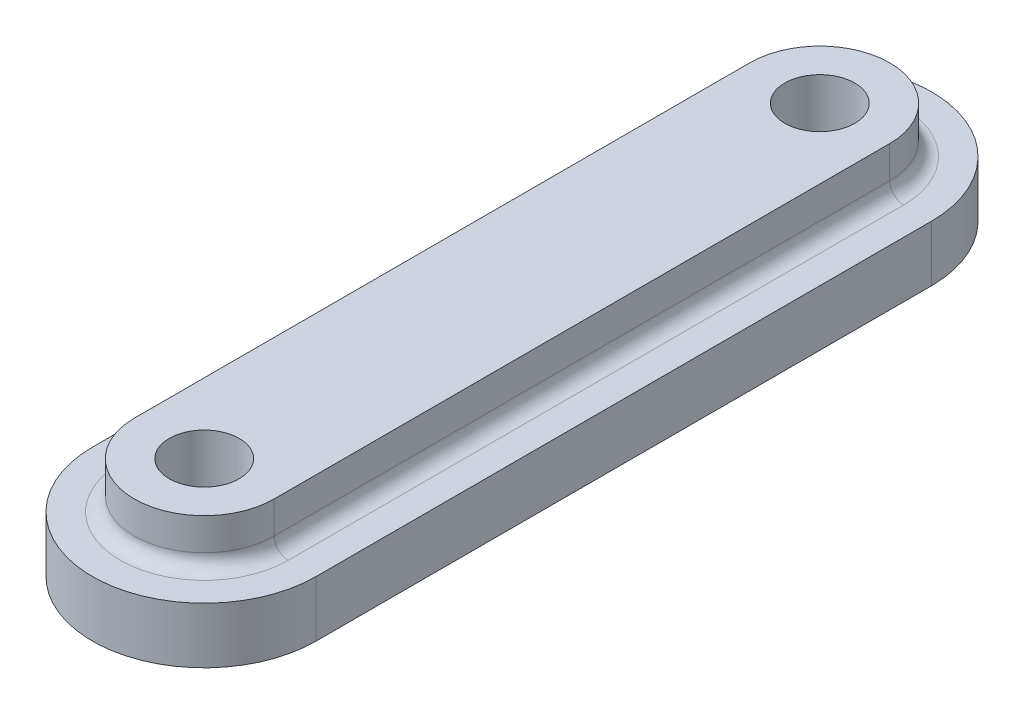
SolidWorks part; units mm, degrees
ref_plane "Front Plane" through (0, 0, 0) normal (0, 0, 1) x (1, 0, 0)
ref_plane "Top Plane" through (0, 0, 0) normal (0, 1, 0) x (1, 0, 0)
ref_plane "Right Plane" through (0, 0, 0) normal (1, 0, 0) x (0, 0, -1)
ref_plane "Plane1" through (0, -0.825, 0) normal (0, 1, 0) x (1, 0, 0)
sketch "Sketch1" plane through (0, -0.825, 0) normal (0, 1, 0) x (1, 0, 0)
  line L0 (42, -11) -> (42, 11)
  line L1 (34, 11) -> (34, -11)
  arc A0 (42, 11) -> (34, 11) centre (38, 11) ccw
  arc A1 (34, -11) -> (42, -11) centre (38, -11) ccw
extrude "Boss-Extrude1" add sketch "Sketch1" against normal blind 2
sketch "Sketch2" plane through (0, -0.825, 0) normal (0, 1, 0) x (-1, 0, 0)
  line L0 (-35.5, 11) -> (-35.5, -11)
  line L1 (-40.5, -11) -> (-40.5, 11)
  arc A0 (-35.5, -11) -> (-40.5, -11) centre (-38, -11) cw
  arc A1 (-40.5, 11) -> (-35.5, 11) centre (-38, 11) cw
extrude "Boss-Extrude2" add sketch "Sketch2" along normal blind 1.65
hole_wizard "Ø2.5 (2.5) Diameter Hole1" positions "Sketch4" profile "Sketch3" hole size "Ø2.5" standard "ANSI Metric"
sketch "Sketch4" plane through (0, 0.825, 0) normal (0, 1, 0) x (1, 0, 0)
  point P0 (38, -11)
  point P1 (38, 11)
sketch "Sketch3" plane through (38, 0.825, 11) normal (1, 0, 0) x (0, 0, 1)
  line L0 (0, 0) -> (0, 3.65)
  line L1 (0, 3.65) -> (1.25, 3.65)
  line L2 (1.25, 3.65) -> (1.25, 0)
  line L5 (1.25, 0) -> (0, 0)
  line L11 (0, -6.35) -> (0, 107.95) construction
  dimension "Thru Hole Dia." = 2.5
  dimension "Thru Hole Depth" = 3.65
fillet "Fillet1" radius 0.5 4 edges at (40.5, -0.825, 0) (38, -0.825, 13.5) (38, -0.825, -13.5) (35.5, -0.825, 0)
